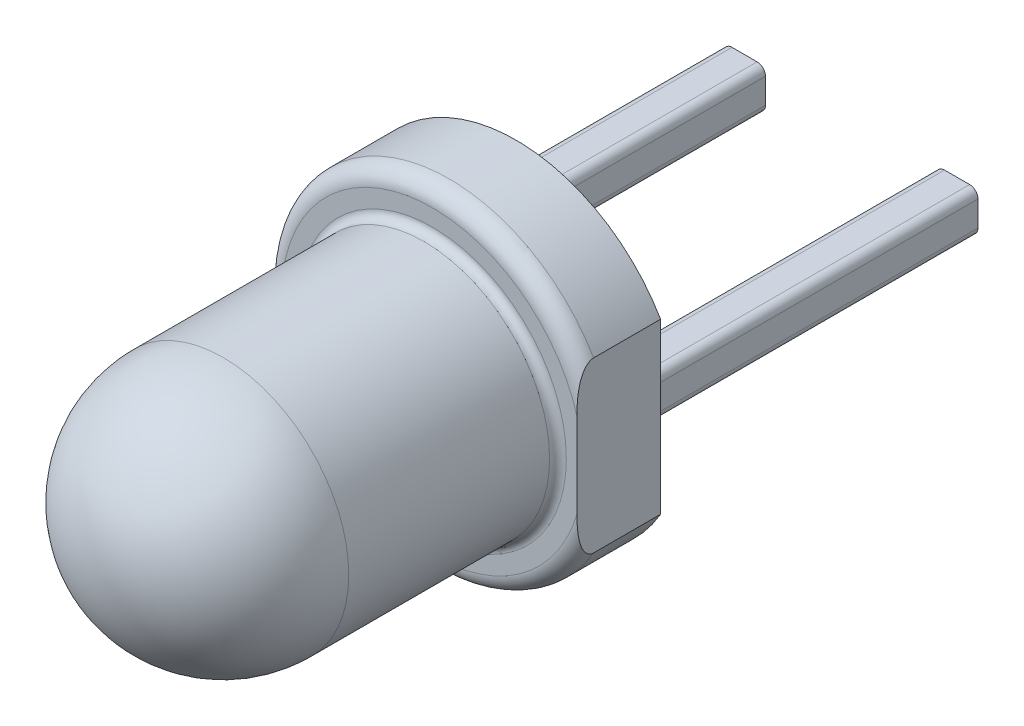
SolidWorks part; units mm, degrees
ref_plane "Front Plane" through (0, 0, 0) normal (0, 0, 1) x (1, 0, 0)
ref_plane "Top Plane" through (0, 0, 0) normal (0, 1, 0) x (1, 0, 0)
ref_plane "Right Plane" through (0, 0, 0) normal (1, 0, 0) x (0, 0, -1)
sketch "Sketch1" plane through (0, 0, 0) normal (0, 0, 1) x (1, 0, 0)
  circle A0 centre (0, 0) radius 2
  dimension "D1" = 4
extrude "Boss-Extrude1" add sketch "Sketch1" along normal blind 1
sketch "Sketch2" plane through (0, 0, 1) normal (0, 0, 1) x (1, 0, 0)
  circle A0 centre (0, 0) radius 1.5
  dimension "D1" = 3
extrude "Boss-Extrude2" add sketch "Sketch2" along normal blind 4
fillet "Fillet1" radius 1.5 1 edges at (1.5, 0, 5)
sketch "Sketch3" plane through (0, 0, 0) normal (0, 0, -1) x (-1, 0, 0)
  line L0 (0, 0) -> (1.3533, 0) construction
  line L1 (0, 0) -> (-1.1388, 0) construction
  line L3 (-1.52, -0.25) -> (-1.02, -0.25)
  line L4 (-1.52, -0.25) -> (-1.52, 0.25)
  line L5 (-1.52, 0.25) -> (-1.02, 0.25)
  line L6 (-1.02, -0.25) -> (-1.02, 0.25)
  line L7 (-1.52, -0.25) -> (-1.02, 0.25) construction
  line L8 (-1.52, 0.25) -> (-1.02, -0.25) construction
  line L9 (1.02, -0.25) -> (1.52, -0.25)
  line L10 (1.02, -0.25) -> (1.02, 0.25)
  line L11 (1.02, 0.25) -> (1.52, 0.25)
  line L12 (1.52, -0.25) -> (1.52, 0.25)
  line L13 (1.02, -0.25) -> (1.52, 0.25) construction
  line L14 (1.02, 0.25) -> (1.52, -0.25) construction
  point P3 (-1.27, 0)
  point P9 (1.27, 0)
  dimension "D1" = 0.5
  dimension "D2" = 0.5
  dimension "D3" = 0.5
  dimension "D4" = 0.5
  dimension "D5" = 1.27
  dimension "D6" = 1.27
extrude "Boss-Extrude3" add sketch "Sketch3" along normal blind 4
fillet "Fillet2" radius 0.2 1 edges at (2, 0, 1)
fillet "Fillet3" radius 0.1 1 edges at (1.5, 0, 1)
fillet "Fillet4" radius 0.1 8 edges at (-1.52, 0.25, -2) (1.02, 0.25, -2) (-1.52, -0.25, -2) (-1.02, -0.25, -2) (-1.02, 0.25, -2) (1.02, -0.25, -2) (1.52, 0.25, -2) (1.52, -0.25, -2)
sketch "Sketch5" plane through (0, 0, 0) normal (0, 0, -1) x (-1, 0, 0)
  line L0 (-1.7266, 1.0093) -> (-1.7266, -1.0093)
  circle A0 centre (0, 0) radius 2 construction
  circle A2 centre (0, 0) radius 2
  circle M9 centre (0, 0) radius 2
  dimension "D2" = 2.0186
extrude "Cut-Extrude1" cut sketch "Sketch5" against normal through all contours L0 M9
